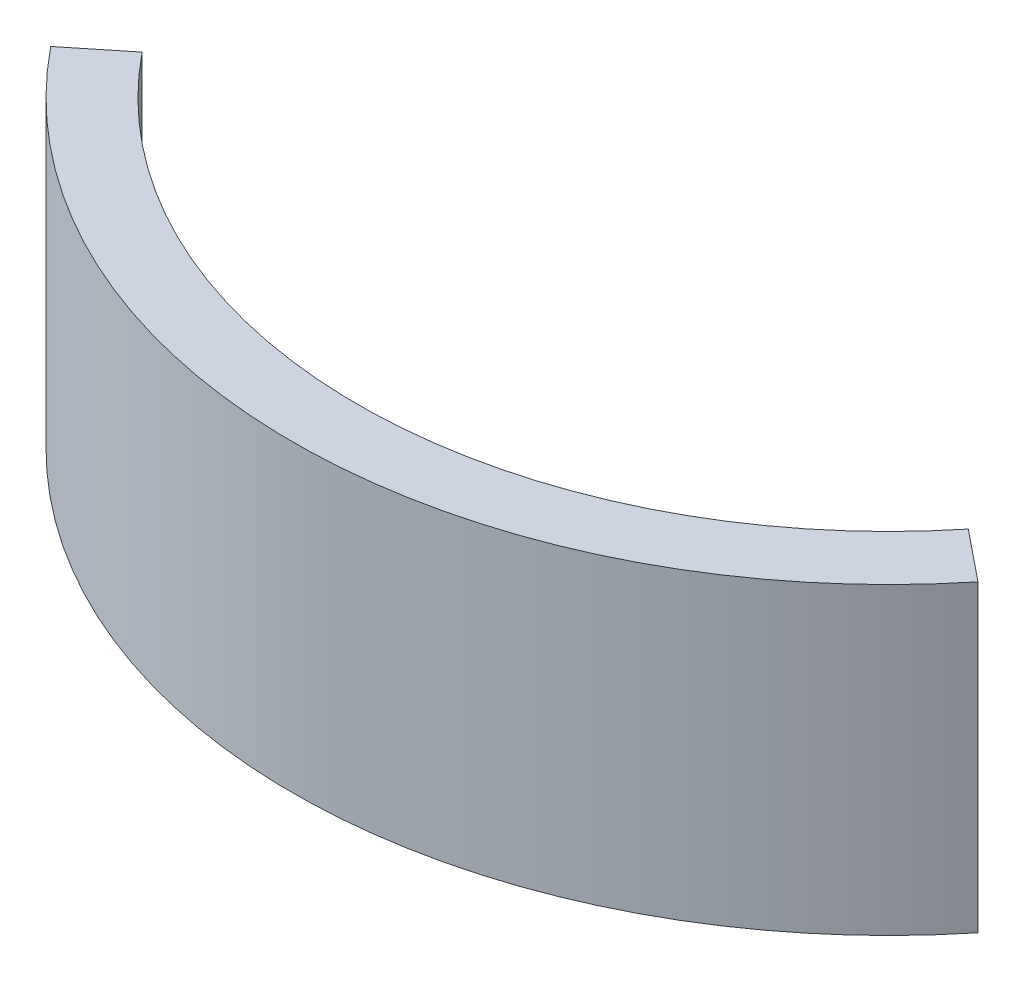
SolidWorks part; units mm, degrees
ref_plane "Front Plane" through (0, 0, 0) normal (0, 0, 1) x (1, 0, 0)
ref_plane "Top Plane" through (0, 0, 0) normal (0, 1, 0) x (1, 0, 0)
ref_plane "Right Plane" through (0, 0, 0) normal (1, 0, 0) x (0, 0, -1)
sketch "Sketch1" plane through (0, 0, 0) normal (0, 1, 0) x (1, 0, 0)
  line L0 (9.274, 4.4314) -> (8.2626, 5.2481)
  line L1 (-8.2626, 5.2481) -> (-9.274, 4.4314)
  arc A0 (-9.274, 4.4314) -> (9.274, 4.4314) centre (0, 11.92) ccw
  arc A1 (-8.2626, 5.2481) -> (8.2626, 5.2481) centre (0, 11.92) ccw
  dimension "D1" = 11.92
  dimension "D2" = 10.62
  dimension "D3" = 8.2626
  dimension "D4" = 4.4314
extrude "Boss-Extrude1" add sketch "Sketch1" along normal blind 6.08
